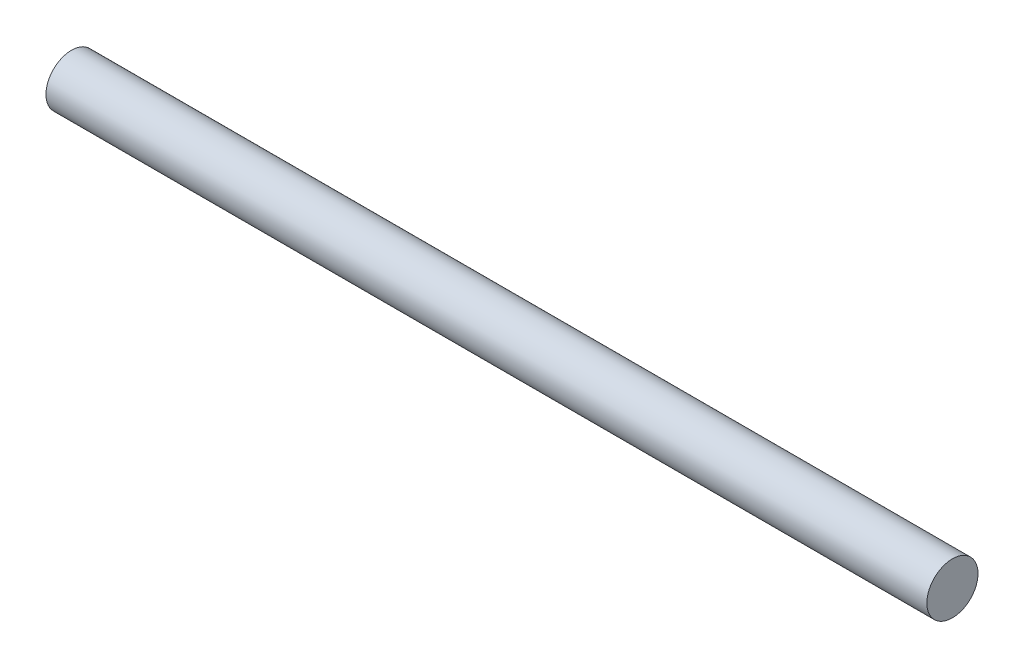
SolidWorks part; units mm, degrees
ref_plane "Plan de face" through (0, 0, 0) normal (0, 0, 1) x (1, 0, 0)
ref_plane "Plan de dessus" through (0, 0, 0) normal (0, 1, 0) x (1, 0, 0)
ref_plane "Plan de droite" through (0, 0, 0) normal (1, 0, 0) x (0, 0, -1)
sketch "Esquisse5" plane through (0, 0, 0) normal (1, 0, 0) x (0, 0, -1)
  circle A0 centre (0, 0) radius 18
extrude "Boss.-Extru.3" add sketch "Esquisse5" along normal blind 620
ref_plane "Plan2" through (10, 0, 0) normal (-1, 0, 0) x (0, 0, 1)
ref_plane "Plan4" through (610, 0, 0) normal (-1, 0, 0) x (0, 0, 1)
sketch "Esquisse6" plane through (10, 0, 0) normal (-1, 0, 0) x (0, 0, 1)
  circle A0 centre (0, 0) radius 18
sketch "Esquisse7" plane through (610, 0, 0) normal (-1, 0, 0) x (0, 0, 1)
  circle A0 centre (0, 0) radius 18
ref_plane "Plan65" through (530, 0, 0) normal (-1, 0, 0) x (0, 0, 1)
ref_plane "Plan67" through (470, 0, 0) normal (-1, 0, 0) x (0, 0, 1)
ref_plane "Plan68" through (450, 0, 0) normal (-1, 0, 0) x (0, 0, 1)
ref_plane "Plan69" through (430, 0, 0) normal (-1, 0, 0) x (0, 0, 1)
ref_plane "Plan70" through (410, 0, 0) normal (-1, 0, 0) x (0, 0, 1)
ref_plane "Plan71" through (350, 0, 0) normal (-1, 0, 0) x (0, 0, 1)
ref_plane "Plan72" through (270, 0, 0) normal (-1, 0, 0) x (0, 0, 1)
ref_plane "Plan73" through (210, 0, 0) normal (-1, 0, 0) x (0, 0, 1)
ref_plane "Plan74" through (190, 0, 0) normal (-1, 0, 0) x (0, 0, 1)
ref_plane "Plan75" through (170, 0, 0) normal (-1, 0, 0) x (0, 0, 1)
ref_plane "Plan76" through (150, 0, 0) normal (-1, 0, 0) x (0, 0, 1)
ref_plane "Plan79" through (90, 0, 0) normal (-1, 0, 0) x (0, 0, 1)
sketch "Esquisse70" plane through (530, 0, 0) normal (-1, 0, 0) x (0, 0, 1)
  circle A0 centre (0, 0) radius 18
sketch "Esquisse71" plane through (470, 0, 0) normal (-1, 0, 0) x (0, 0, 1)
  circle A0 centre (0, 0) radius 18
sketch "Esquisse72" plane through (450, 0, 0) normal (-1, 0, 0) x (0, 0, 1)
  circle A0 centre (0, 0) radius 18
sketch "Esquisse73" plane through (430, 0, 0) normal (-1, 0, 0) x (0, 0, 1)
  circle A0 centre (0, 0) radius 18
sketch "Esquisse74" plane through (410, 0, 0) normal (-1, 0, 0) x (0, 0, 1)
  circle A0 centre (0, 0) radius 18
sketch "Esquisse75" plane through (350, 0, 0) normal (-1, 0, 0) x (0, 0, 1)
  circle A0 centre (0, 0) radius 18
sketch "Esquisse76" plane through (270, 0, 0) normal (-1, 0, 0) x (0, 0, 1)
  circle A0 centre (0, 0) radius 18
sketch "Esquisse77" plane through (210, 0, 0) normal (-1, 0, 0) x (0, 0, 1)
  circle A0 centre (0, 0) radius 18
sketch "Esquisse78" plane through (190, 0, 0) normal (-1, 0, 0) x (0, 0, 1)
  circle A0 centre (0, 0) radius 18
sketch "Esquisse79" plane through (170, 0, 0) normal (-1, 0, 0) x (0, 0, 1)
  circle A0 centre (0, 0) radius 18
sketch "Esquisse80" plane through (150, 0, 0) normal (-1, 0, 0) x (0, 0, 1)
  circle A0 centre (0, 0) radius 18
sketch "Esquisse81" plane through (90, 0, 0) normal (-1, 0, 0) x (0, 0, 1)
  circle A0 centre (0, 0) radius 18
